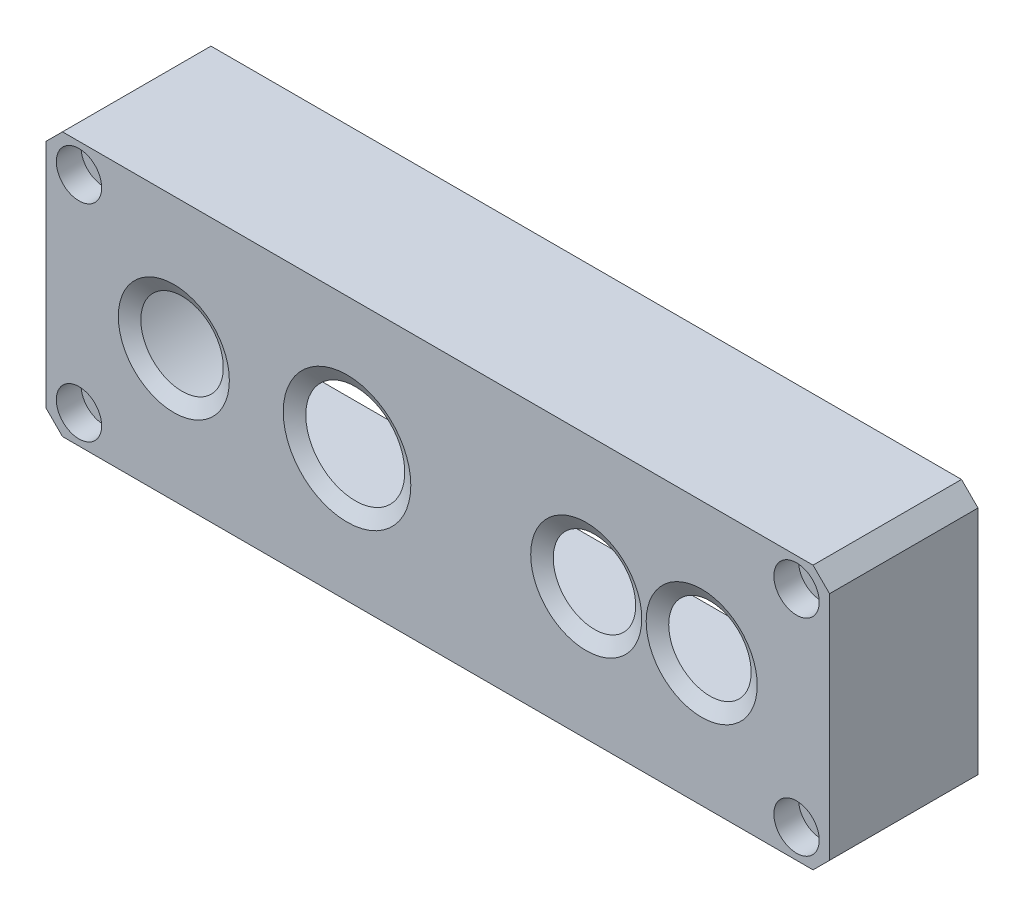
SolidWorks part; units mm, degrees
material "ABS"
ref_plane "前视基准面" through (0, 0, 0) normal (0, 0, 1) x (1, 0, 0)
ref_plane "上视基准面" through (0, 0, 0) normal (0, 1, 0) x (1, 0, 0)
ref_plane "右视基准面" through (0, 0, 0) normal (1, 0, 0) x (0, 0, -1)
other "Configuration Table"
sketch "草图1" plane through (0, 0, 0) normal (0, 0, 1) x (1, 0, 0)
  line L0 (-218.4627, 92.6239) -> (-151.4627, 92.6239) construction
  line L1 (-183.9627, 108.1239) -> (-183.9627, 76.1239) construction
  line L6 (-229.4627, 108.1239) -> (-138.4627, 108.1239)
  line L7 (-231.4627, 106.1239) -> (-231.4627, 78.1239)
  line L10 (-218.4627, 105.1239) -> (-151.4627, 105.1239) construction
  line L11 (-218.4627, 80.1239) -> (-151.4627, 80.1239) construction
  line L33 (-229.4627, 76.1239) -> (-138.4627, 76.1239)
  line L34 (-136.4627, 106.1239) -> (-136.4627, 78.1239)
  line L35 (-231.4627, 108.1239) -> (-136.4627, 76.1239) construction
  line L36 (-231.4627, 76.1239) -> (-136.4627, 108.1239) construction
  line L37 (-231.4627, 106.1239) -> (-229.4627, 108.1239)
  line L38 (-231.4627, 78.1239) -> (-229.4627, 76.1239)
  line L39 (-138.4627, 76.1239) -> (-136.4627, 78.1239)
  line L40 (-138.4627, 108.1239) -> (-136.4627, 106.1239)
  line L41 (-228.6343, 106.1239) -> (-139.2911, 106.1239)
  line L42 (-139.2911, 106.1239) -> (-138.4627, 105.2955)
  line L43 (-138.4627, 105.2955) -> (-138.4627, 78.9524)
  line L44 (-139.2911, 78.1239) -> (-138.4627, 78.9524)
  line L45 (-228.6343, 78.1239) -> (-139.2911, 78.1239)
  line L46 (-229.4627, 78.9524) -> (-228.6343, 78.1239)
  line L47 (-229.4627, 105.2955) -> (-229.4627, 78.9524)
  line L48 (-229.4627, 105.2955) -> (-228.6343, 106.1239)
  arc A0 (-218.4627, 105.1239) -> (-218.4627, 80.1239) centre (-218.4627, 92.6239) ccw construction
  arc A1 (-151.4627, 80.1239) -> (-151.4627, 105.1239) centre (-151.4627, 92.6239) ccw construction
  point P2 (-181.9095, 38.4345)
  point P7 (-184.9627, 92.6239)
  point P12 (-183.9627, 92.1239)
  dimension "D2" = 3
  dimension "D7" = 2.5
  dimension "D1" = 92
  dimension "D3" = 25
  dimension "D4" = 95
  dimension "D5" = 32
  dimension "D6" = 2
extrude "凸台-拉伸1" add sketch "草图1" against normal blind 17
sketch "草图2" plane through (0, 0, 0) normal (0, 0, 1) x (1, 0, 0)
  line L0 (-231.4627, 92.1239) -> (-136.4627, 92.1239) construction
  line L1 (-215.9627, 92.1239) -> (-151.9627, 92.1239) construction
  line L2 (-215.9627, 102.1239) -> (-151.9627, 102.1239) construction
  line L3 (-215.9627, 82.1239) -> (-151.9627, 82.1239) construction
  line L4 (-136.4627, 106.1239) -> (-136.4627, 78.1239) construction
  line L5 (-216.4627, 92.1239) -> (-151.4627, 92.1239) construction
  line L6 (-216.4627, 104.6239) -> (-151.4627, 104.6239) construction
  line L7 (-216.4627, 79.6239) -> (-151.4627, 79.6239) construction
  line L8 (-136.4627, 106.1239) -> (-138.4627, 108.1239)
  line L9 (-136.4627, 106.1239) -> (-138.4627, 108.1239)
  line L10 (-138.4627, 108.1239) -> (-229.4627, 108.1239)
  line L11 (-138.4627, 108.1239) -> (-229.4627, 108.1239)
  line L12 (-229.4627, 108.1239) -> (-231.4627, 106.1239)
  line L13 (-229.4627, 108.1239) -> (-231.4627, 106.1239)
  line L14 (-231.4627, 106.1239) -> (-231.4627, 78.1239)
  line L15 (-231.4627, 106.1239) -> (-231.4627, 78.1239)
  line L24 (-183.9627, 92.1239) -> (-183.9627, 108.1239) construction
  line L33 (-231.4627, 78.1239) -> (-229.4627, 76.1239)
  line L34 (-231.4627, 78.1239) -> (-229.4627, 76.1239)
  line L35 (-229.4627, 76.1239) -> (-138.4627, 76.1239)
  line L36 (-229.4627, 76.1239) -> (-138.4627, 76.1239)
  line L37 (-138.4627, 76.1239) -> (-136.4627, 78.1239)
  line L38 (-138.4627, 76.1239) -> (-136.4627, 78.1239)
  line L39 (-136.4627, 78.1239) -> (-136.4627, 106.1239)
  line L40 (-136.4627, 78.1239) -> (-136.4627, 106.1239)
  circle A0 centre (-194.9627, 92.1239) radius 6
  circle A1 centre (-165.9627, 92.1239) radius 5
  circle A2 centre (-215.9627, 92.1239) radius 5
  arc A4 (-215.9627, 102.1239) -> (-215.9627, 82.1239) centre (-215.9627, 92.1239) ccw construction
  arc A5 (-151.9627, 82.1239) -> (-151.9627, 102.1239) centre (-151.9627, 92.1239) ccw construction
  arc A6 (-216.4627, 104.6239) -> (-216.4627, 79.6239) centre (-216.4627, 92.1239) ccw construction
  arc A7 (-151.4627, 79.6239) -> (-151.4627, 104.6239) centre (-151.4627, 92.1239) ccw construction
  circle A8 centre (-226.9627, 103.6239) radius 1.25 construction
  circle A9 centre (-226.9627, 103.6239) radius 2.5 construction
  circle A10 centre (-140.9627, 80.6239) radius 1.25 construction
  circle A11 centre (-140.9627, 80.6239) radius 2.5 construction
  circle A12 centre (-151.9627, 92.1239) radius 5
  point P17 (-183.9627, 92.1239)
  point P24 (-183.9627, 92.1239)
  dimension "D2" = 10
  dimension "D4" = 84
  dimension "D5" = 90
  dimension "D7" = 21
  dimension "D8" = 10
  dimension "D9" = 12
  dimension "D12" = 2.5
  dimension "D13" = 5
  dimension "D16" = 2
  dimension "D19" = 10
  dimension "D20" = 64
  dimension "D3" = 50
  dimension "D6" = 25
  dimension "D14" = 2
  dimension "D15" = 2
  dimension "D17" = 2
  dimension "D1" = 0
extrude "凸台-拉伸2" add sketch "草图2" along normal blind 1
sketch "草图3" plane through (0, 0, 0) normal (0, 0, -1) x (-1, 0, 0)
  circle A0 centre (151.9627, 92.1239) radius 5 construction
  circle A1 centre (151.9627, 92.1239) radius 5
  circle A6 centre (215.9627, 92.1239) radius 5 construction
  circle A7 centre (194.9627, 92.1239) radius 6 construction
  circle A8 centre (165.9627, 92.1239) radius 5 construction
  circle A9 centre (215.9627, 92.1239) radius 5
  circle A10 centre (194.9627, 92.1239) radius 6
  circle A11 centre (165.9627, 92.1239) radius 5
extrude "切除-拉伸1" cut sketch "草图3" against normal blind 11 draft 60 draft outward yes
sketch "草图8" plane through (0, 0, 0) normal (0, 0, -1) x (-1, 0, 0)
  line L0 (229.4627, 92.1239) -> (138.4627, 92.1239) construction
  line L1 (229.4627, 105.2955) -> (229.4627, 78.9524) construction
  line L2 (138.4627, 105.2955) -> (138.4627, 78.9524) construction
  line L3 (216.9627, 92.1239) -> (150.9627, 92.1239) construction
  line L4 (216.9627, 79.6239) -> (150.9627, 79.6239)
  line L5 (216.9627, 104.6239) -> (150.9627, 104.6239)
  line L6 (183.9627, 92.1239) -> (183.9627, 76.1239) construction
  line L7 (229.4627, 76.1239) -> (138.4627, 76.1239) construction
  line L16 (229.4627, 78.9524) -> (229.4627, 105.2955)
  line L17 (229.4627, 105.2955) -> (228.6343, 106.1239)
  line L18 (228.6343, 106.1239) -> (139.2911, 106.1239)
  line L19 (139.2911, 106.1239) -> (138.4627, 105.2955)
  line L20 (138.4627, 105.2955) -> (138.4627, 78.9524)
  line L21 (138.4627, 78.9524) -> (139.2911, 78.1239)
  line L22 (139.2911, 78.1239) -> (228.6343, 78.1239)
  line L23 (228.6343, 78.1239) -> (229.4627, 78.9524)
  line L24 (229.4627, 78.9524) -> (229.4627, 105.2955)
  line L25 (229.4627, 105.2955) -> (228.6343, 106.1239)
  line L26 (228.6343, 106.1239) -> (139.2911, 106.1239)
  line L27 (139.2911, 106.1239) -> (138.4627, 105.2955)
  line L28 (138.4627, 105.2955) -> (138.4627, 78.9524)
  line L29 (138.4627, 78.9524) -> (139.2911, 78.1239)
  line L30 (139.2911, 78.1239) -> (228.6343, 78.1239)
  line L31 (228.6343, 78.1239) -> (229.4627, 78.9524)
  arc A0 (216.9627, 79.6239) -> (216.9627, 104.6239) centre (216.9627, 92.1239) ccw
  arc A1 (150.9627, 104.6239) -> (150.9627, 79.6239) centre (150.9627, 92.1239) ccw
  point P8 (183.9627, 92.1239)
  line M14 (229.4627, 78.9524) -> (229.4627, 105.2955)
  line M15 (229.4627, 105.2955) -> (228.6343, 106.1239)
  line M16 (228.6343, 106.1239) -> (139.2911, 106.1239)
  line M17 (139.2911, 106.1239) -> (138.4627, 105.2955)
  line M18 (138.4627, 105.2955) -> (138.4627, 78.9524)
  line M19 (138.4627, 78.9524) -> (139.2911, 78.1239)
  line M20 (139.2911, 78.1239) -> (228.6343, 78.1239)
  line M21 (228.6343, 78.1239) -> (229.4627, 78.9524)
  dimension "D2" = 91
  dimension "D1" = 25
  dimension "D3" = 0
extrude "凸台-拉伸5" add sketch "草图8" along normal up to surface (17 mm away) contours A1 L28 A0 L4 M19 M20 M21 M14 | A1 L5 A0 L24 M15 M16 M17 M18 up to face at (-183.9627, 92.1239, -17)
sketch "草图9" plane through (0, 0, -17) normal (0, 0, -1) x (-1, 0, 0)
  line L0 (229.4627, 76.1239) -> (138.4627, 76.1239) construction
  line L1 (231.4627, 106.1239) -> (231.4627, 78.1239) construction
  line L2 (183.9627, 76.1239) -> (183.9627, 108.1239) construction
  line L3 (229.4627, 108.1239) -> (138.4627, 108.1239) construction
  line L4 (231.4627, 92.1239) -> (136.4627, 92.1239) construction
  line L5 (136.4627, 106.1239) -> (136.4627, 78.1239) construction
  circle A0 centre (227.4627, 79.6239) radius 1.3
  circle A1 centre (227.4627, 104.6239) radius 1.3
  circle A2 centre (140.4627, 79.6239) radius 1.3
  circle A3 centre (140.4627, 104.6239) radius 1.3
  dimension "D1" = 2.6
  dimension "D2" = 3.5
  dimension "D3" = 4
extrude "切除-拉伸6" cut sketch "草图9" against normal through all
sketch "草图10" plane through (0, 0, 1) normal (0, 0, 1) x (1, 0, 0)
  circle A0 centre (-227.4627, 104.6239) radius 2.75
  circle A1 centre (-140.4627, 104.6239) radius 2.75
  circle A2 centre (-227.4627, 79.6239) radius 2.75
  circle A3 centre (-140.4627, 79.6239) radius 2.75
  circle A4 centre (-140.4627, 104.6239) radius 1.3 construction
  circle A5 centre (-140.4627, 79.6239) radius 1.3 construction
  circle A6 centre (-227.4627, 104.6239) radius 1.3 construction
  circle A7 centre (-227.4627, 79.6239) radius 1.3 construction
  dimension "D1" = 5.5
extrude "切除-拉伸7" cut sketch "草图10" against normal blind 3
